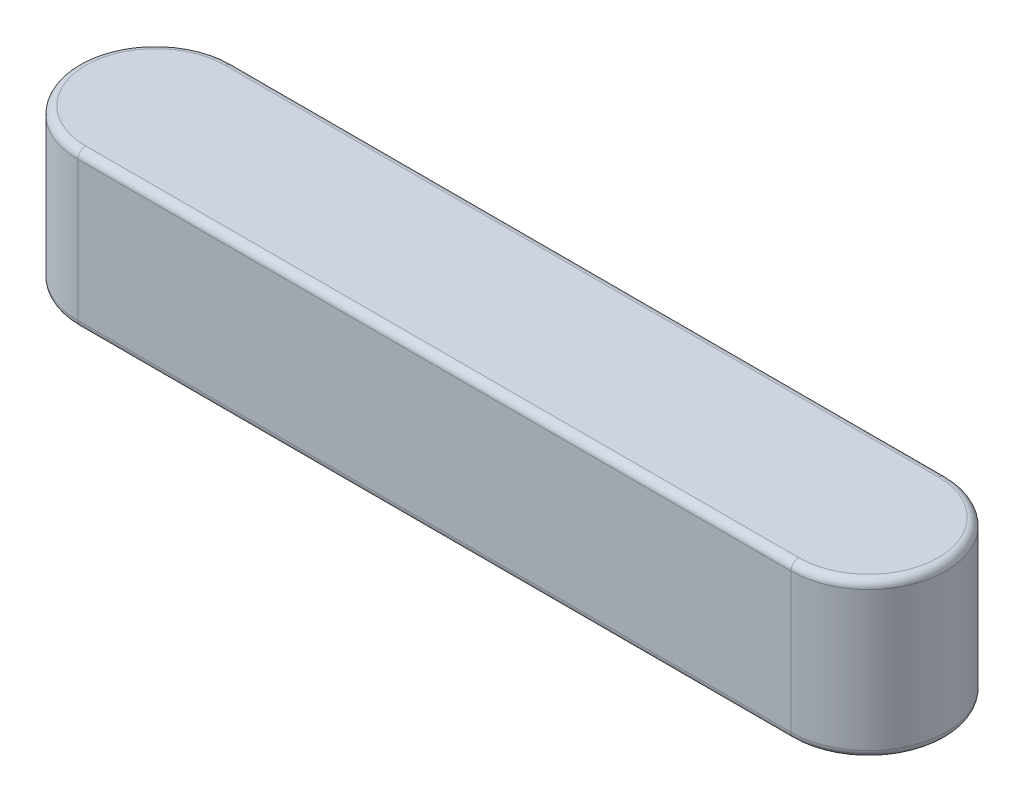
SolidWorks part; units mm, degrees
ref_plane "Front Plane" through (0, 0, 0) normal (0, 0, 1) x (1, 0, 0)
ref_plane "Top Plane" through (0, 0, 0) normal (0, 1, 0) x (1, 0, 0)
ref_plane "Right Plane" through (0, 0, 0) normal (1, 0, 0) x (0, 0, -1)
other "Configuration Table"
sketch "Sketch1" plane through (0, 0, 0) normal (0, 1, 0) x (1, 0, 0)
  line L1 (-23, 2.5) -> (0, 2.5)
  line L3 (-23, -2.5) -> (0, -2.5)
  arc A0 (0, -2.5) -> (0, 2.5) centre (0, 0) ccw
  arc A1 (-23, 2.5) -> (-23, -2.5) centre (-23, 0) ccw
  dimension "l" = 28
  dimension "b" = 5
extrude "Extrude1" add sketch "Sketch1" along normal blind 5
fillet "Fillet1" radius 0.25 8 edges at (-11.5, 0, -2.5) (2.5, 0, 0) (-25.5, 0, 0) (-11.5, 0, 2.5) (2.5, 5, 0) (-11.5, 5, 2.5) (-11.5, 5, -2.5) (-25.5, 5, 0)
